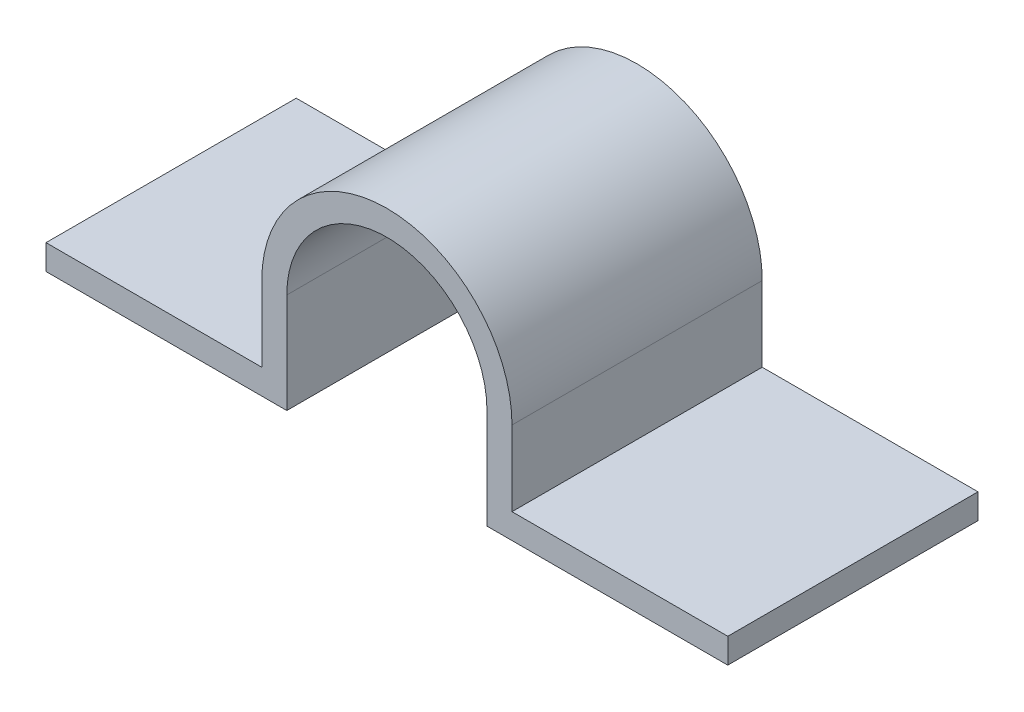
SolidWorks part; units mm, degrees
material "镀铬不锈钢"
ref_plane "前视基准面" through (0, 0, 0) normal (0, 0, 1) x (1, 0, 0)
ref_plane "上视基准面" through (0, 0, 0) normal (0, 1, 0) x (1, 0, 0)
ref_plane "右视基准面" through (0, 0, 0) normal (1, 0, 0) x (0, 0, -1)
sketch "草图1" plane through (0, 0, 0) normal (0, 0, 1) x (1, 0, 0)
  line L0 (0, 0) -> (0, 16.5455) construction
  line L1 (5, 4) -> (5, 1)
  line L2 (5, 1) -> (13.6233, 1)
  line L3 (13.6233, 1) -> (13.6233, 0)
  line L4 (13.6233, 0) -> (4, 0)
  line L5 (4, 4) -> (4, 0)
  line L6 (0, 0) -> (18.8515, 0) construction
  line L7 (-4, 4) -> (-4, 0)
  line L8 (-13.6233, 0) -> (-4, 0)
  line L9 (-13.6233, 1) -> (-13.6233, 0)
  line L10 (-5, 1) -> (-13.6233, 1)
  line L11 (-5, 4) -> (-5, 1)
  arc A0 (5, 4) -> (-5, 4) centre (0, 4) ccw
  arc A1 (4, 4) -> (-4, 4) centre (0, 4) ccw
  dimension "D1" = 10
  dimension "D2" = 1
  dimension "D3" = 1
  dimension "D4" = 4
extrude "凸台-拉伸1" add sketch "草图1" along normal blind 10 contours A1 L7 L8 L9 L10 L11 A0 L1 L2 L3 L4 L5
